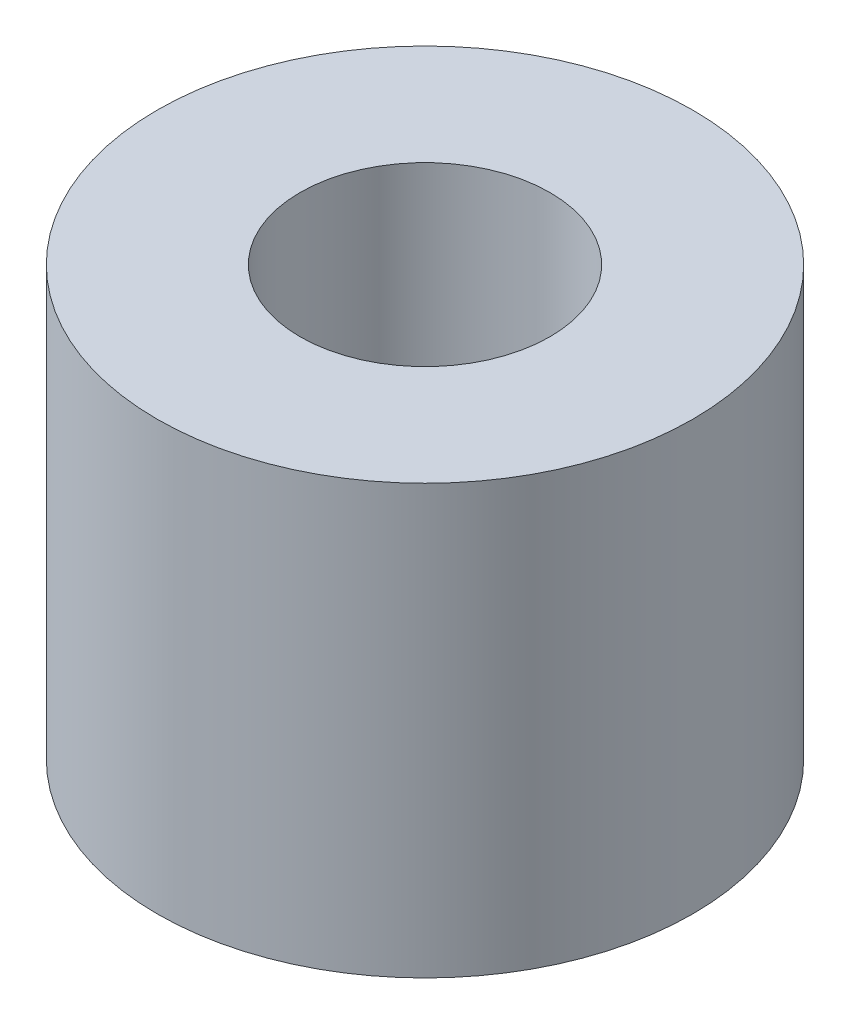
SolidWorks part; units mm, degrees
ref_plane "Front Plane" through (0, 0, 0) normal (0, 0, 1) x (1, 0, 0)
ref_plane "Top Plane" through (0, 0, 0) normal (0, 1, 0) x (1, 0, 0)
ref_plane "Right Plane" through (0, 0, 0) normal (1, 0, 0) x (0, 0, -1)
sketch "Sketch1" plane through (0, 0, 0) normal (0, 1, 0) x (1, 0, 0)
  circle A0 centre (0, 0) radius 1.75
  circle A1 centre (0, 0) radius 3.75
  dimension "D1" = 3.5
  dimension "D2" = 2
extrude "Boss-Extrude1" add sketch "Sketch1" along normal blind 6
